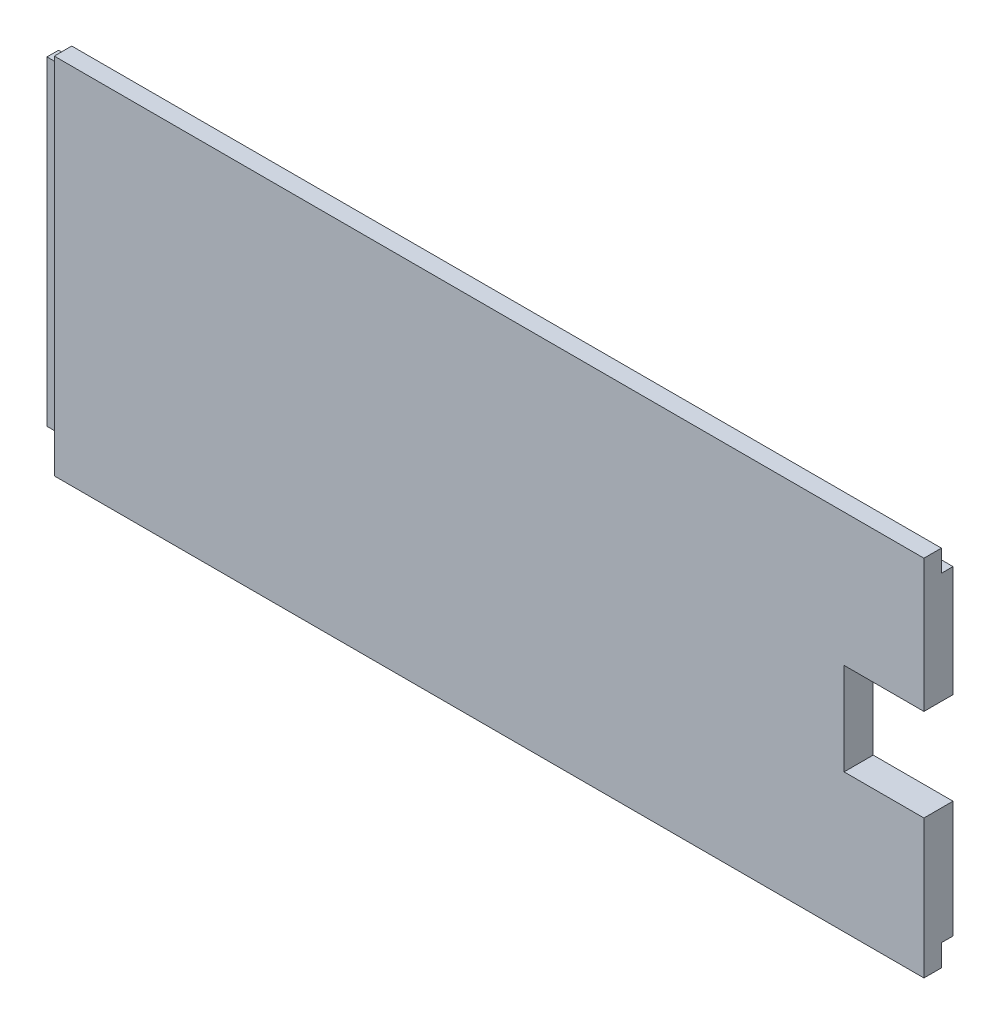
SolidWorks part; units mm, degrees
ref_plane "Front Plane" through (0, 0, 0) normal (0, 0, 1) x (1, 0, 0)
ref_plane "Top Plane" through (0, 0, 0) normal (0, 1, 0) x (1, 0, 0)
ref_plane "Right Plane" through (0, 0, 0) normal (1, 0, 0) x (0, 0, -1)
sketch "Sketch3" plane through (0, 0, 0) normal (0, 0, 1) x (1, 0, 0)
  line L0 (115.8399, 50.5231) -> (153.9148, 50.5231) construction
  line L1 (-2.2952, -5.3569) -> (153.9148, -5.3569)
  line L2 (-2.2952, -5.3569) -> (-2.2952, 50.5231)
  line L3 (-2.2952, 50.5231) -> (153.9148, 50.5231)
  line L4 (153.9148, -5.3569) -> (153.9148, 50.5231)
  dimension "D1" = 156.21
extrude "Boss-Extrude2" add sketch "Sketch3" along normal blind 2.032
sketch "Sketch4" plane through (0, 0, 2.032) normal (0, 0, 1) x (1, 0, 0)
  line L6 (1.5148, 54.3331) -> (153.9148, 54.3331) construction
  line L11 (2.0261, 54.3331) -> (153.9148, 54.3331)
  line L12 (2.0261, 54.3331) -> (2.0261, -9.1669)
  line L13 (2.0261, -9.1669) -> (153.9148, -9.1669)
  line L14 (153.9148, 54.3331) -> (153.9148, -9.1669)
extrude "Boss-Extrude3" add sketch "Sketch4" along normal blind 3.048
sketch "Sketch5" plane through (0, 0, 5.08) normal (0, 0, 1) x (1, 0, 0)
  line L1 (153.9148, 15.0372) -> (139.973, 15.0372)
  line L2 (153.9148, 15.0372) -> (153.9148, 31.1487)
  line L3 (153.9148, 31.1487) -> (139.973, 31.1487)
  line L4 (139.973, 15.0372) -> (139.973, 31.1487)
  point P4 (143.758, 18.0391)
  point P5 (139.973, 15.0372)
extrude "Cut-Extrude1" cut sketch "Sketch5" against normal through all
